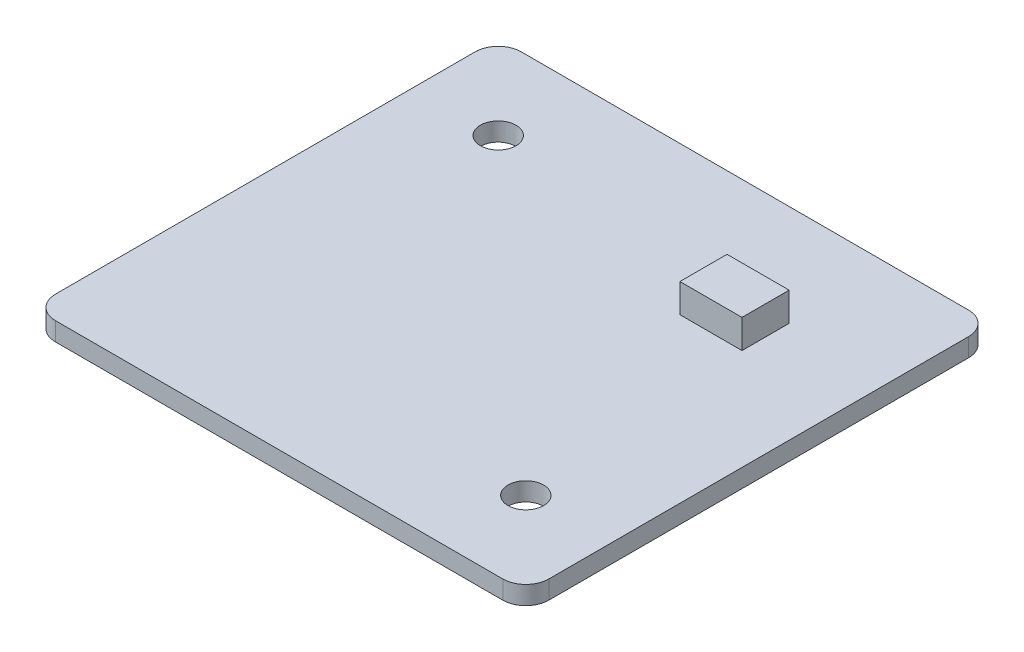
SolidWorks part; units mm, degrees
ref_plane "Front Plane" through (0, 0, 0) normal (0, 0, 1) x (1, 0, 0)
ref_plane "Top Plane" through (0, 0, 0) normal (0, 1, 0) x (1, 0, 0)
ref_plane "Right Plane" through (0, 0, 0) normal (1, 0, 0) x (0, 0, -1)
sketch "Sketch1" plane through (0, 0, 0) normal (0, 1, 0) x (1, 0, 0)
  line L1 (-30.2693, 29.3551) -> (12.6307, 29.3551)
  line L2 (-30.2693, 29.3551) -> (-30.2693, -11.1449)
  line L3 (-30.2693, -11.1449) -> (12.6307, -11.1449)
  line L4 (12.6307, 29.3551) -> (12.6307, -11.1449)
  circle A0 centre (-22.9693, 22.0551) radius 1.55
  circle A1 centre (5.3307, -3.8449) radius 1.55
  dimension "D3" = 7.3
  dimension "D7" = 3.1
  dimension "D1" = 42.9
  dimension "D2" = 40.5
  dimension "D4" = 7.3
  dimension "D5" = 7.3
  dimension "D6" = 7.3
extrude "Boss-Extrude1" add sketch "Sketch1" along normal blind 1.6
fillet "Fillet1" radius 2 4 edges at (-30.2693, 0.8, 11.1449) (12.6307, 0.8, -29.3551) (12.6307, 0.8, 11.1449) (-30.2693, 0.8, -29.3551)
sketch "Sketch2" plane through (0, 1.6, 0) normal (0, 1, 0) x (1, 0, 0)
  line L0 (10.6307, 29.3551) -> (-28.2693, 29.3551) construction
  line L1 (-1.5693, 20.5551) -> (3.8307, 20.5551)
  line L2 (-1.5693, 20.5551) -> (-1.5693, 16.4551)
  line L3 (-1.5693, 16.4551) -> (3.8307, 16.4551)
  line L4 (3.8307, 20.5551) -> (3.8307, 16.4551)
  line L5 (12.6307, -9.1449) -> (12.6307, 27.3551) construction
  dimension "D1" = 5.4
  dimension "D2" = 4.1
  dimension "D3" = 8.8
  dimension "D4" = 8.8
extrude "Boss-Extrude2" add sketch "Sketch2" along normal blind 2.5
sketch "Sketch3" plane through (0, 0, 0) normal (0, -1, 0) x (1, 0, 0)
  line L0 (-28.2693, 11.1449) -> (10.6307, 11.1449) construction
  line L1 (-21.6693, 5.8949) -> (-1.1693, 5.8949)
  line L2 (-21.6693, 5.8949) -> (-21.6693, 3.3349)
  line L3 (-21.6693, 3.3349) -> (-1.1693, 3.3349)
  line L4 (-1.1693, 5.8949) -> (-1.1693, 3.3349)
  line L5 (12.6307, 9.1449) -> (12.6307, -27.3551) construction
  dimension "D1" = 20.5
  dimension "D2" = 2.56
  dimension "D3" = 5.25
  dimension "D4" = 13.8
extrude "Boss-Extrude3" add sketch "Sketch3" along normal blind 2.3
